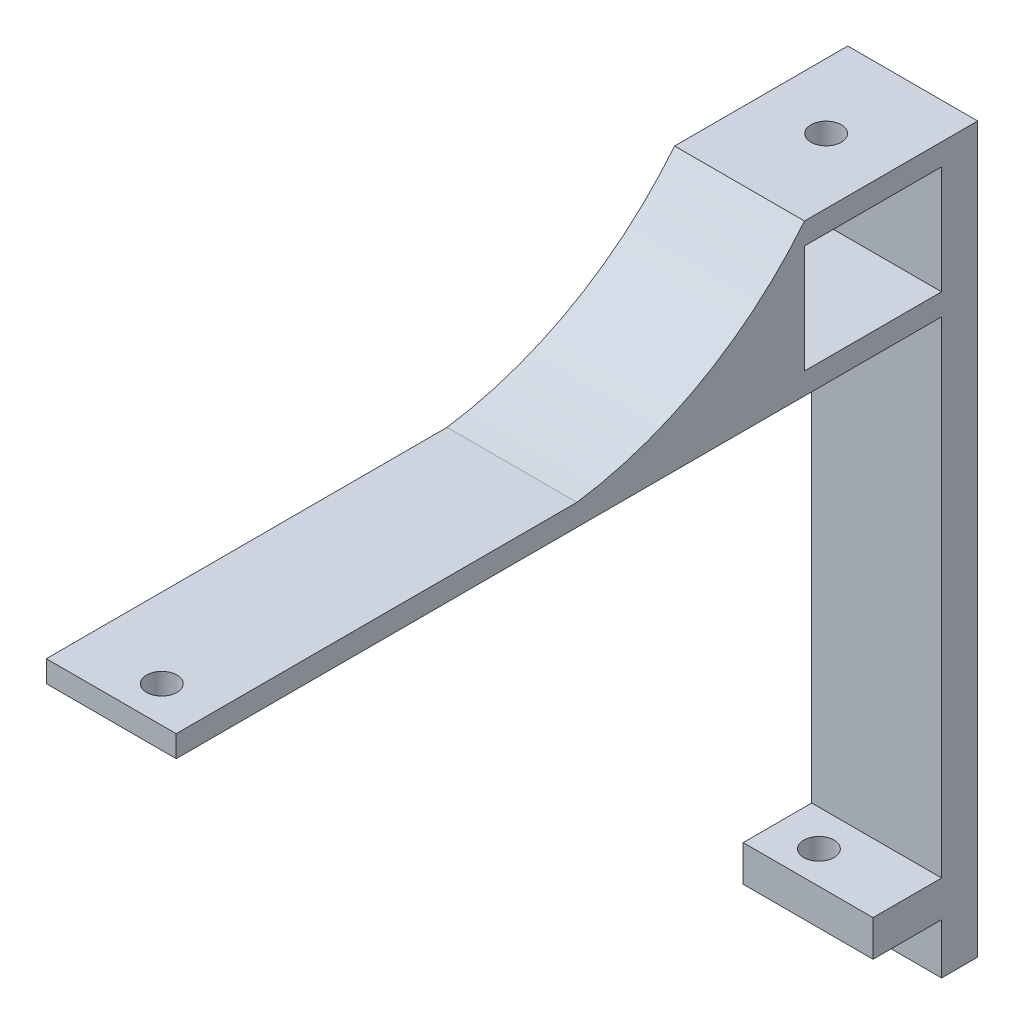
SolidWorks part; units mm, degrees
ref_plane "Front Plane" through (0, 0, 0) normal (0, 0, 1) x (1, 0, 0)
ref_plane "Top Plane" through (0, 0, 0) normal (0, 1, 0) x (1, 0, 0)
ref_plane "Right Plane" through (0, 0, 0) normal (1, 0, 0) x (0, 0, -1)
sketch "Sketch3" plane through (0, 0, 0) normal (1, 0, 0) x (0, 0, -1)
  line L1 (22.6396, 117.064) -> (32.6396, 117.064)
  line L2 (22.6396, 117.064) -> (22.6396, 192.4144)
  line L3 (22.6396, 192.4144) -> (32.6396, 192.4144)
  line L4 (32.6396, 117.064) -> (32.6396, 192.4144)
  line L6 (-73.4248, 192.4144) -> (22.6396, 192.4144)
  line L8 (-73.4248, 189.4144) -> (22.6396, 189.4144)
  line L9 (22.6396, 192.4144) -> (22.6396, 189.4144)
  line L10 (-63.4248, 192.4144) -> (-63.4248, 189.4144)
  line L11 (-73.4248, 192.4144) -> (-73.4248, 189.4144)
  line L12 (37.6396, 117.064) -> (32.6396, 117.064)
  line L13 (32.6396, 192.4144) -> (37.6396, 192.4144)
  line L14 (32.6396, 192.4144) -> (32.6396, 110.064)
  line L15 (32.6396, 110.064) -> (37.6396, 110.064)
  line L16 (37.6396, 192.4144) -> (37.6396, 110.064)
  line L17 (32.6396, 122.064) -> (22.6396, 122.064)
  dimension "D1" = 10
  dimension "D2" = 0
  dimension "D3" = 10
  dimension "D4" = 5
  dimension "D5" = 5
sketch "Sketch4" plane through (0, 0, 0) normal (1, 0, 0) x (0, 0, -1)
  line L1 (22.6396, 122.064) -> (32.6396, 122.064)
  line L2 (22.6396, 122.064) -> (22.6396, 117.064)
  line L3 (22.6396, 117.064) -> (32.6396, 117.064)
  line L4 (32.6396, 122.064) -> (32.6396, 117.064)
  line L5 (37.6396, 110.064) -> (32.6396, 110.064)
  line L6 (37.6396, 110.064) -> (37.6396, 192.4144)
  line L7 (37.6396, 192.4144) -> (32.6396, 192.4144)
  line L8 (32.6396, 110.064) -> (32.6396, 192.4144)
  line L9 (-73.4248, 192.4144) -> (32.6396, 192.4144)
  line L10 (-73.4248, 192.4144) -> (-73.4248, 189.4144)
  line L11 (-73.4248, 189.4144) -> (32.6396, 189.4144)
  line L12 (32.6396, 192.4144) -> (32.6396, 189.4144)
extrude "Boss-Extrude1" add sketch "Sketch4" along normal blind 52 contours L10 L11 L8 L9 | L8 L5 L6 L7 L4 | L4 L1 L2 L3
sketch "Sketch5" plane through (0, 122.064, 0) normal (0, 1, 0) x (1, 0, 0)
  line L0 (26, 22.6396) -> (26, 32.6396) construction
  line L1 (52, 22.6396) -> (0, 22.6396) construction
  line L2 (52, 32.6396) -> (0, 32.6396) construction
  circle A0 centre (6, 27.0496) radius 2.1
  circle A1 centre (46, 27.6396) radius 2.1
  dimension "D1" = 4.2
  dimension "D2" = 4.2
  dimension "D3" = 20
  dimension "D4" = 20
  dimension "D5" = 4.41
  dimension "D6" = 5
extrude "Cut-Extrude1" cut sketch "Sketch5" against normal blind 52
sketch "Sketch6" plane through (0, 192.4144, 0) normal (0, 1, 0) x (1, 0, 0)
  line L0 (52, -73.4248) -> (0, -73.4248) construction
  line L1 (26, -73.4248) -> (26, -63.8952) construction
  circle A0 centre (41, -68.4248) radius 2.1
  circle A1 centre (11, -68.4248) radius 2.1
  dimension "D1" = 4.2
  dimension "D2" = 5
  dimension "D3" = 15
extrude "Cut-Extrude2" cut sketch "Sketch6" against normal blind 52
sketch "Sketch7" plane through (0, 0, -37.6396) normal (0, 0, -1) x (-1, 0, 0)
  line L0 (-26, 192.4144) -> (-26, 110.064) construction
  line L1 (-52, 192.4144) -> (0, 192.4144) construction
  line L2 (-52, 110.064) -> (0, 110.064) construction
  line L3 (-18, 192.4144) -> (-18, 110.064)
  line L4 (-18, 192.4144) -> (-34, 192.4144)
  line L5 (-26, 192.4144) -> (-26, 110.064)
  line L6 (-18, 110.064) -> (-34, 110.064)
  line L7 (-34, 192.4144) -> (-34, 110.064)
  line M9 (-52, 110.064) -> (0, 110.064)
  dimension "D1" = 8
extrude "Cut-Extrude4" cut sketch "Sketch7" against normal blind 124 contours L4 L7 L5 M9
sketch "Sketch8" plane through (0, 0, 0) normal (-1, 0, 0) x (0, 0, 1)
  line L0 (-37.6396, 192.4144) -> (-37.6396, 210.4144)
  line L1 (-37.6396, 210.4144) -> (-13.6396, 210.4144)
  line L2 (73.4248, 192.4144) -> (-37.6396, 192.4144) construction
  line L3 (-37.6396, 192.4144) -> (17.8926, 192.4144)
  line L4 (-32.6396, 192.4144) -> (-32.6396, 207.4144)
  line L5 (-32.6396, 207.4144) -> (-13.6396, 207.4144)
  line L6 (-13.6396, 207.4144) -> (-13.6396, 192.4144)
  arc A0 (-13.6396, 210.4144) -> (17.8926, 192.4144) centre (25.0593, 241.5878) ccw
  line M8 (73.4248, 192.4144) -> (-37.6396, 192.4144)
  dimension "D1" = 18
  dimension "D2" = 24
  dimension "D3" = 5
  dimension "D4" = 3
extrude "Boss-Extrude2" add sketch "Sketch8" against normal up to surface (18 mm away) contours A0 L1 L0 L3 L4 L5 L6 M8 up to face at (18, 146.2041, -10.4267)
sketch "Sketch9" plane through (0, 210.4144, 0) normal (0, 1, 0) x (1, 0, 0)
  line L0 (9, 13.6396) -> (9, 37.6396) construction
  line L1 (18, 13.6396) -> (0, 13.6396) construction
  line L2 (18, 37.6396) -> (0, 37.6396) construction
  line L3 (0, 25.6396) -> (18, 25.6396) construction
  line L4 (0, 37.6396) -> (0, 13.6396) construction
  line L5 (18, 37.6396) -> (18, 13.6396) construction
  circle A0 centre (9, 25.6396) radius 2.1
  dimension "D1" = 4.2
extrude "Cut-Extrude5" cut sketch "Sketch9" against normal blind 6
sketch "Sketch11" plane through (52, 0, 0) normal (1, 0, 0) x (0, 0, -1)
  line L0 (32.6396, 192.4144) -> (37.6396, 192.4144)
  line L1 (37.6396, 192.4144) -> (37.6396, 210.4144)
  line L2 (37.6396, 210.4144) -> (13.6396, 210.4144)
  line L3 (32.6396, 192.4144) -> (32.6396, 207.4144)
  line L4 (32.6396, 207.4144) -> (13.6396, 207.4144)
  line L5 (13.6396, 207.4144) -> (13.6396, 192.4144)
  line L6 (13.6396, 192.4144) -> (-17.8926, 192.4144)
  line L7 (-73.4248, 192.4144) -> (37.6396, 192.4144) construction
  arc A0 (13.6396, 210.4144) -> (-17.8926, 192.4144) centre (-25.0593, 241.5878) cw
extrude "Boss-Extrude3" add sketch "Sketch11" against normal up to surface (18 mm away) up to face at (34, 146.2041, -10.4267)
sketch "Sketch12" plane through (0, 210.4144, 0) normal (0, 1, 0) x (1, 0, 0)
  line L0 (43, 37.6396) -> (43, 13.6396) construction
  line L1 (34, 37.6396) -> (52, 37.6396) construction
  line L2 (34, 13.6396) -> (52, 13.6396) construction
  line L3 (34, 25.6396) -> (52, 25.6396) construction
  line L4 (34, 13.6396) -> (34, 37.6396) construction
  line L5 (52, 37.6396) -> (52, 13.6396) construction
  circle A0 centre (43, 25.6396) radius 2.1
  dimension "D1" = 4.2
extrude "Cut-Extrude7" cut sketch "Sketch12" against normal blind 11
sketch "Sketch13" plane through (0, 210.4144, 0) normal (0, 1, 0) x (1, 0, 0)
  line L1 (-6.2363, 41.7302) -> (24.5227, 41.7302)
  line L2 (-6.2363, 41.7302) -> (-6.2363, -77.0804)
  line L3 (-6.2363, -77.0804) -> (24.5227, -77.0804)
  line L4 (24.5227, 41.7302) -> (24.5227, -77.0804)
extrude "Cut-Extrude8" cut sketch "Sketch13" against normal blind 134
sketch "Sketch14" plane through (0, 122.064, 0) normal (0, 1, 0) x (1, 0, 0)
  line L1 (34, 32.6396) -> (52, 32.6396)
  line L2 (34, 32.6396) -> (34, 22.6396)
  line L3 (34, 22.6396) -> (52, 22.6396)
  line L4 (52, 32.6396) -> (52, 22.6396)
  dimension "D1" = 10
extrude "Boss-Extrude4" add sketch "Sketch14" against normal blind 5
sketch "Sketch15" plane through (0, 122.064, 0) normal (0, 1, 0) x (1, 0, 0)
  line L0 (34, 27.6396) -> (60, 27.6396) construction
  line L1 (34, 22.6396) -> (34, 32.6396) construction
  line L2 (52, 32.6396) -> (34, 32.6396) construction
  circle A0 centre (40, 27.0496) radius 2.1
  dimension "D2" = 4.2
  dimension "D3" = 5.59
  dimension "D4" = 20
  dimension "D1" = 26
extrude "Cut-Extrude9" cut sketch "Sketch15" against normal blind 10
sketch "Sketch16" plane through (0, 192.4144, 0) normal (0, 1, 0) x (1, 0, 0)
  line L0 (34, -67.7294) -> (60, -67.7294) construction
  line L1 (34, -73.4248) -> (34, -17.8926) construction
  circle A1 centre (41, -68.4248) radius 2.1
  dimension "D1" = 26
extrude "Boss-Extrude5" add sketch "Sketch16" against normal up to surface (3 mm away) up to face at (41, 189.4144, 70.5248)
sketch "Sketch17" plane through (0, 192.4144, 0) normal (0, 1, 0) x (1, 0, 0)
  line L1 (34, -65.216) -> (60, -65.216) construction
  line L2 (34, -73.4248) -> (34, -17.8926) construction
  line L3 (52, -73.4248) -> (34, -73.4248) construction
  circle A0 centre (45, -68.4248) radius 2.1
  dimension "D1" = 4.2
  dimension "D2" = 26
  dimension "D3" = 5
  dimension "D4" = 15
extrude "Cut-Extrude10" cut sketch "Sketch17" against normal blind 68
sketch "Sketch18" plane through (0, 122.064, 0) normal (0, 1, 0) x (1, 0, 0)
  line L0 (52, 22.6396) -> (52, 32.6396) construction
  line L1 (34, 22.6396) -> (52, 22.6396)
  line L2 (34, 22.6396) -> (34, 23.1396)
  line L3 (34, 23.1396) -> (52, 23.1396)
  line L4 (52, 22.6396) -> (52, 23.1396)
  dimension "D1" = 0.5
extrude "Cut-Extrude11" cut sketch "Sketch18" against normal blind 68
sketch "Sketch19" plane through (0, 122.064, 0) normal (0, 1, 0) x (1, 0, 0)
  line L1 (36.804, 30.0811) -> (43.8678, 30.0811)
  line L2 (36.804, 30.0811) -> (36.804, 24.5083)
  line L3 (36.804, 24.5083) -> (43.8678, 24.5083)
  line L4 (43.8678, 30.0811) -> (43.8678, 24.5083)
extrude "Boss-Extrude6" add sketch "Sketch19" against normal up to surface (5 mm away) up to face at (40, 117.064, -24.9496)
sketch "Sketch20" plane through (0, 122.064, 0) normal (0, 1, 0) x (1, 0, 0)
  line L0 (52, 32.6396) -> (34, 32.6396) construction
  line L1 (34, 27.8896) -> (60, 27.8896) construction
  line L2 (34, 23.1396) -> (34, 32.6396) construction
  circle A0 centre (40, 27.6396) radius 2.1
  dimension "D1" = 4.2
  dimension "D2" = 5
  dimension "D4" = 20
  dimension "D3" = 26
extrude "Cut-Extrude12" cut sketch "Sketch20" against normal blind 10
